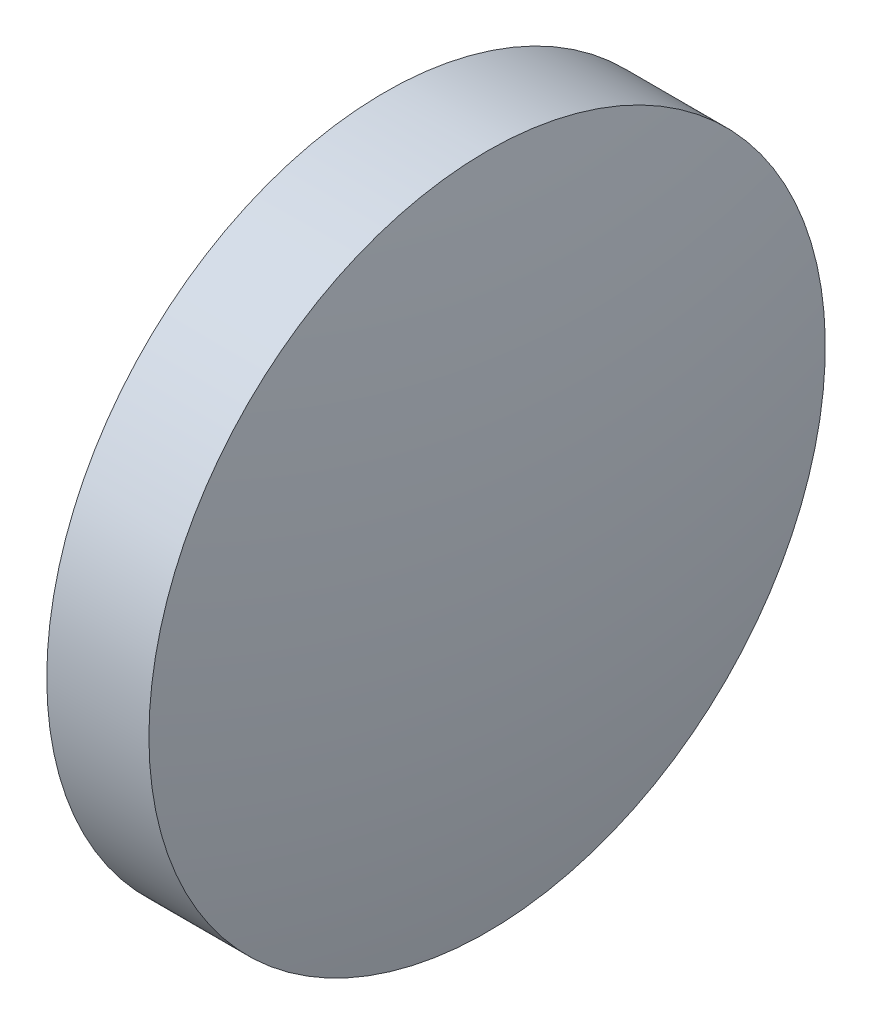
SolidWorks part; units mm, degrees
ref_plane "前视基准面" through (0, 0, 0) normal (0, 0, 1) x (1, 0, 0)
ref_plane "上视基准面" through (0, 0, 0) normal (0, 1, 0) x (1, 0, 0)
ref_plane "右视基准面" through (0, 0, 0) normal (1, 0, 0) x (0, 0, -1)
sketch "草图2" plane through (0, 0, 0) normal (0, 0, 1) x (1, 0, 0)
  line L0 (462.5679, 129.064) -> (468.1685, 129.064) construction
  line L1 (463.3656, 129.064) -> (463.3656, 134.064)
  line L2 (465.3656, 129.064) -> (463.3656, 129.064)
  line L5 (463.3656, 134.064) -> (464.8756, 134.064)
  arc A0 (465.3656, 129.064) -> (464.8756, 134.064) centre (439.6104, 129.064) ccw
revolve "旋转2" add sketch "草图2" angle 360 about L0
